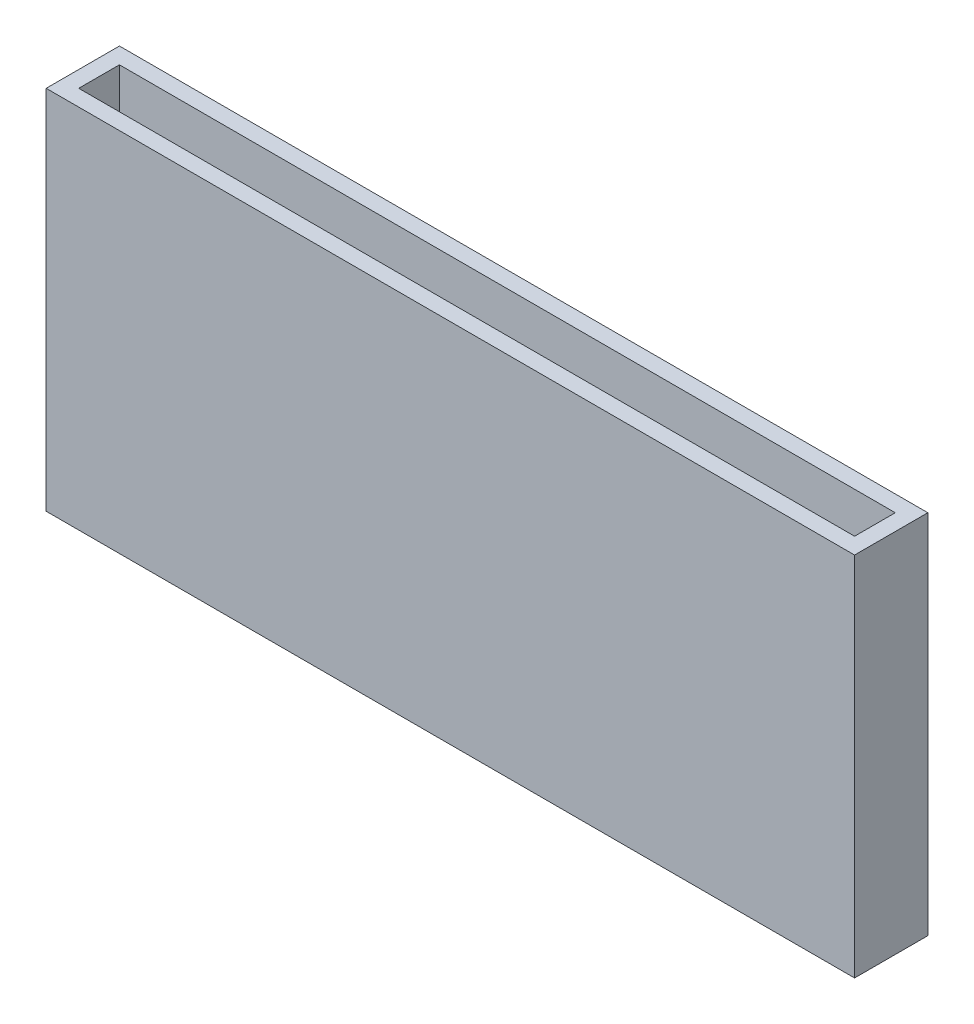
SolidWorks part; units mm, degrees
ref_plane "Front Plane" through (0, 0, 0) normal (0, 0, 1) x (1, 0, 0)
ref_plane "Top Plane" through (0, 0, 0) normal (0, 1, 0) x (1, 0, 0)
ref_plane "Right Plane" through (0, 0, 0) normal (1, 0, 0) x (0, 0, -1)
sketch "Sketch1" plane through (0, 0, 0) normal (0, 0, 1) x (1, 0, 0)
  line L1 (0, 90) -> (198.6214, 90)
  line L2 (0, 90) -> (0, 0)
  line L3 (0, 0) -> (198.6214, 0)
  line L4 (198.6214, 90) -> (198.6214, 0)
  point P4 (0, 0)
  point P5 (198.6214, 90)
  dimension "D1" = 90
extrude "Boss-Extrude1" add sketch "Sketch1" along normal blind 4
sketch "Sketch3" plane through (0, 0, 4) normal (0, 0, 1) x (1, 0, 0)
  line L0 (198.6214, 90) -> (0, 90) construction
  line L1 (0, 0) -> (4, 0)
  line L2 (0, 0) -> (0, 90)
  line L3 (0, 90) -> (4, 90)
  line L4 (4, 0) -> (4, 90)
  line L5 (198.6214, 0) -> (198.6214, 90) construction
  line L6 (198.6214, 90) -> (194.6214, 90)
  line L7 (198.6214, 90) -> (198.6214, 0)
  line L8 (198.6214, 0) -> (194.6214, 0)
  line L9 (194.6214, 90) -> (194.6214, 0)
  line L10 (0, 0) -> (198.6214, 0) construction
  dimension "D1" = 4
  dimension "D2" = 4
extrude "Boss-Extrude2" add sketch "Sketch3" along normal blind 10
sketch "Sketch21" plane through (0, 0, 14) normal (0, 0, 1) x (1, 0, 0)
  line L0 (0, -7.7) -> (0, 7.7) construction
  line L1 (0, 90) -> (198.6214, 90)
  line L2 (0, 90) -> (0, 0)
  line L3 (0, 0) -> (198.6214, 0)
  line L4 (198.6214, 90) -> (198.6214, 0)
  line L5 (4, 90) -> (0, 90) construction
extrude "Boss-Extrude3" add sketch "Sketch21" along normal blind 4
sketch "Sketch22" plane through (0, 0, 0) normal (0, 0, -1) x (-1, 0, 0)
  line L0 (0, 0) -> (-198.6214, 0) construction
  line L1 (-198.6214, 90) -> (-194.6214, 90)
  line L2 (-198.6214, 90) -> (-198.6214, 0)
  line L3 (-198.6214, 0) -> (-194.6214, 0)
  line L4 (-194.6214, 90) -> (-194.6214, 0)
  dimension "D1" = 4
